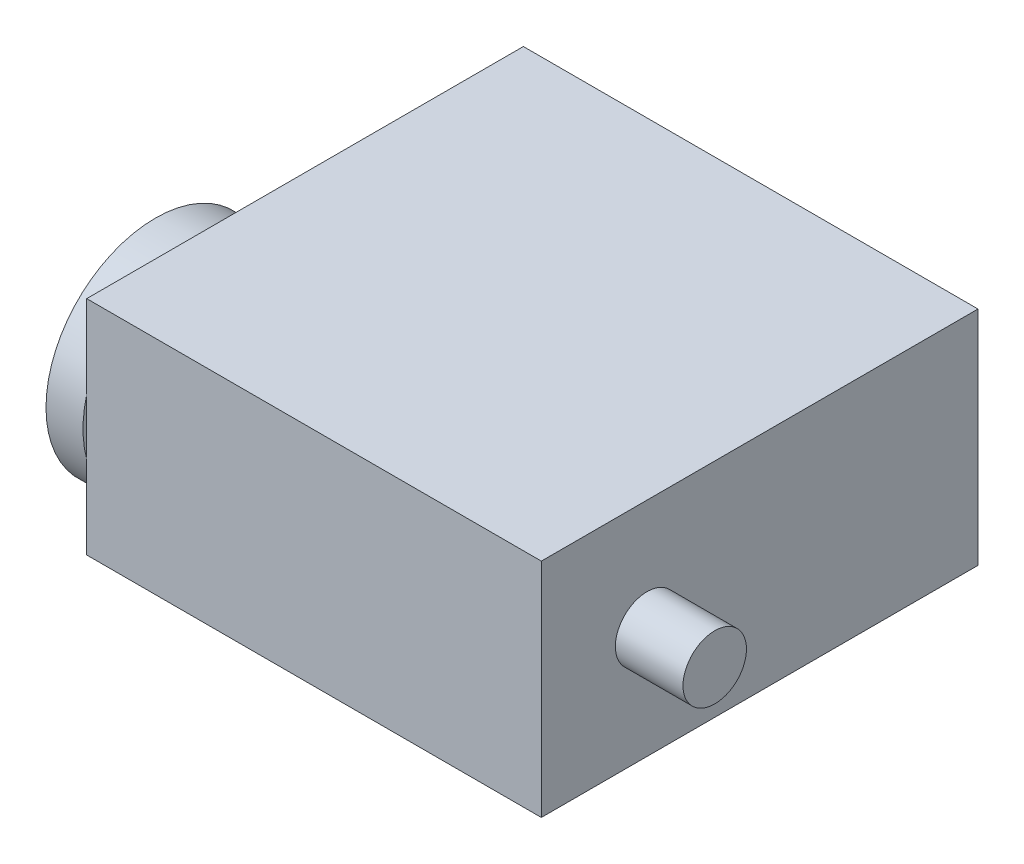
SolidWorks part; units mm, degrees
ref_plane "前视基准面" through (0, 0, 0) normal (0, 0, 1) x (1, 0, 0)
ref_plane "上视基准面" through (0, 0, 0) normal (0, 1, 0) x (1, 0, 0)
ref_plane "右视基准面" through (0, 0, 0) normal (1, 0, 0) x (0, 0, -1)
sketch "草图1" plane through (0, 0, 0) normal (0, 0, 1) x (1, 0, 0)
  line L1 (21.5, 10.5) -> (-21.5, 10.5)
  line L2 (21.5, 10.5) -> (21.5, -10.5)
  line L3 (21.5, -10.5) -> (-21.5, -10.5)
  line L4 (-21.5, 10.5) -> (-21.5, -10.5)
  line L5 (21.5, 10.5) -> (-21.5, -10.5) construction
  line L6 (21.5, -10.5) -> (-21.5, 10.5) construction
  point P0 (0, 0)
  dimension "D1" = 43
  dimension "D2" = 21
extrude "凸台-拉伸1" add sketch "草图1" along normal blind 41.3
sketch "草图2" plane through (21.5, 0, 0) normal (1, 0, 0) x (0, 0, -1)
  line L0 (-41.3, -10.5) -> (-41.3, 10.5) construction
  line L1 (-31.3, 0) -> (0, 0) construction
  circle A0 centre (-31.3, 0) radius 3
  dimension "D1" = 6
  dimension "D2" = 10
extrude "凸台-拉伸2" add sketch "草图2" along normal blind 6.4
sketch "草图3" plane through (-21.5, 0, 0) normal (-1, 0, 0) x (0, 0, 1)
  circle A0 centre (31.3, 0) radius 10.35
extrude "凸台-拉伸3" add sketch "草图3" along normal offset from surface (3.5 mm away) 46.5 up to face at (21.5, 0, 20.65)
sketch "草图4" plane through (-25, 0, 0) normal (-1, 0, 0) x (0, 0, 1)
  circle A0 centre (31.3, 0) radius 6
extrude "凸台-拉伸4" add sketch "草图4" along normal blind 1.5
sketch "草图5" plane through (-25, 0, 0) normal (-1, 0, 0) x (0, 0, 1)
  circle A0 centre (38.75, 0) radius 0.75
  circle A1 centre (31.3, 0) radius 6 construction
  circle A2 centre (31.3, -7.45) radius 0.75
  circle A3 centre (23.85, 0) radius 0.75
  circle A4 centre (31.3, 7.45) radius 0.75
  point P13 (31.3, 0)
  dimension "D1" = 1.5
  dimension "D2" = 7.45
  dimension "D3" = 4
extrude "切除-拉伸1" cut sketch "草图5" against normal blind 4
